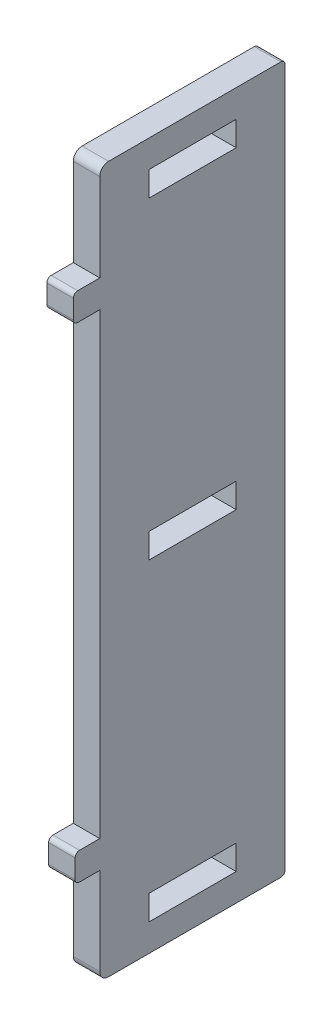
SolidWorks part; units mm, degrees
ref_plane "Спереди" through (0, 0, 0) normal (0, 0, 1) x (1, 0, 0)
ref_plane "Сверху" through (0, 0, 0) normal (0, 1, 0) x (1, 0, 0)
ref_plane "Справа" through (0, 0, 0) normal (1, 0, 0) x (0, 0, -1)
sketch "Эскиз1" plane through (0, 0, 0) normal (1, 0, 0) x (0, 0, -1)
  line L0 (-4.95, 1.4) -> (4.95, 1.4)
  line L1 (-10.5, -40) -> (10.5, -40)
  line L2 (-10.5, -40) -> (-10.5, -29.06)
  line L3 (-10.5, 40) -> (10.5, 40)
  line L4 (10.5, -40) -> (10.5, 40)
  line L5 (-10.5, -40) -> (10.5, 40) construction
  line L6 (-10.5, 40) -> (10.5, -40) construction
  line L7 (-4.95, -34.1) -> (4.95, -34.1)
  line L8 (-4.95, -34.1) -> (-4.95, -36.9)
  line L9 (-4.95, -36.9) -> (4.95, -36.9)
  line L10 (4.95, -34.1) -> (4.95, -36.9)
  line L11 (-4.95, -34.1) -> (4.95, -36.9) construction
  line L12 (-4.95, -36.9) -> (4.95, -34.1) construction
  line L13 (-4.95, 1.4) -> (-4.95, -1.4)
  line L14 (-4.95, -1.4) -> (4.95, -1.4)
  line L15 (4.95, 1.4) -> (4.95, -1.4)
  line L16 (-4.95, 1.4) -> (4.95, -1.4) construction
  line L17 (-4.95, -1.4) -> (4.95, 1.4) construction
  line L18 (-4.95, 36.9) -> (4.95, 36.9)
  line L19 (-4.95, 36.9) -> (-4.95, 34.1)
  line L20 (-4.95, 34.1) -> (4.95, 34.1)
  line L21 (4.95, 36.9) -> (4.95, 34.1)
  line L22 (-4.95, 36.9) -> (4.95, 34.1) construction
  line L23 (-4.95, 34.1) -> (4.95, 36.9) construction
  line L24 (-10.5, -25.94) -> (-10.5, 40)
  line L25 (-13.3, -25.94) -> (-10.5, -25.94)
  line L26 (-13.3, -25.94) -> (-13.3, -29.06)
  line L27 (-13.3, -29.06) -> (-10.5, -29.06)
  line L29 (-13.3, -25.94) -> (-10.5, -29.06) construction
  line L30 (-13.3, -29.06) -> (-10.5, -25.94) construction
  line L32 (-13.5, 29.06) -> (-10.5, 29.06)
  line L33 (-13.5, 29.06) -> (-13.5, 25.94)
  line L34 (-13.5, 25.94) -> (-10.5, 25.94)
  line L35 (-10.5, 29.06) -> (-10.5, 25.94)
  line L36 (-13.5, 29.06) -> (-10.5, 25.94) construction
  line L37 (-13.5, 25.94) -> (-10.5, 29.06) construction
  point P0 (0, 0)
  point P5 (0, 0)
  point P7 (0, -35.5)
  point P16 (0, 35.5)
  point P21 (-12, 27.5)
  point P22 (-11.9, -27.5)
  dimension "D1" = 80
  dimension "D2" = 21
  dimension "D3" = 4.5
  dimension "D4" = 4.5
  dimension "D5" = 9.9
  dimension "D6" = 2.8
  dimension "D7" = 8
  dimension "D9" = 3.12
  dimension "D10" = 3
  dimension "D11" = 8
extrude "Бобышка-Вытянуть1" add sketch "Эскиз1" along normal blind 3 contours L26 L27 L2 L1 L4 L3 L24 L25 L18 L21 L20 L19 L0 L15 L14 L13 L7 L10 L9 L8 | L33 L34 L24 L32
fillet "Скругление1" radius 1 2 edges at (1.5, 40, 10.5) (1.5, -40, 10.5)
fillet "Скругление2" radius 0.5 6 edges at (1.5, -29.06, 13.3) (1.5, -25.94, 13.3) (1.5, 40, -10.5) (1.5, -40, -10.5) (1.5, 25.94, 13.5) (1.5, 29.06, 13.5)
